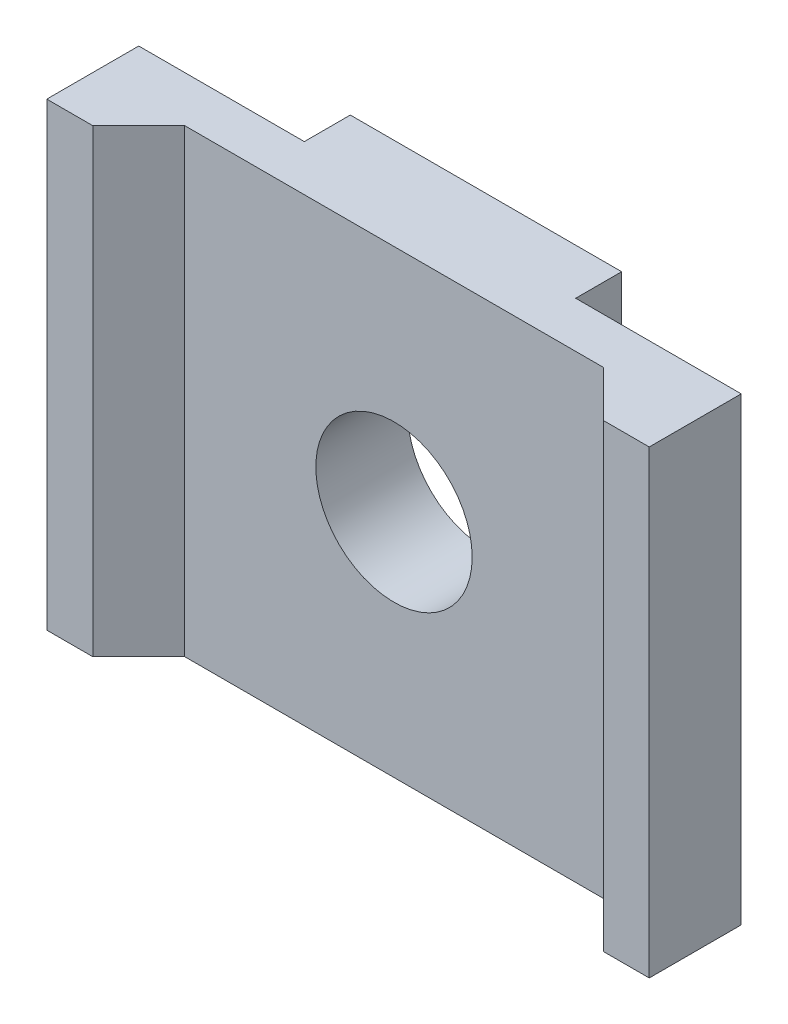
SolidWorks part; units mm, degrees
material "ABS"
ref_plane "Ebene vorne" through (0, 0, 0) normal (0, 0, 1) x (1, 0, 0)
ref_plane "Ebene oben" through (0, 0, 0) normal (0, 1, 0) x (1, 0, 0)
ref_plane "Ebene rechts" through (0, 0, 0) normal (1, 0, 0) x (0, 0, -1)
sketch "Skizze1" plane through (0, 0, 0) normal (0, 1, 0) x (1, 0, 0)
  line L0 (0, 0) -> (-4.55, 0)
  line L1 (-4.55, 0) -> (-4.55, -1)
  line L2 (-4.55, -1) -> (-6.55, -1)
  line L3 (-6.55, -1) -> (-6.55, 1)
  line L4 (-6.55, 1) -> (-2.95, 1)
  line L5 (-2.95, 1) -> (-2.95, 2)
  line L6 (-2.95, 2) -> (0, 2)
  line L7 (0, 2) -> (0, 0)
  dimension "D1" = 2.95
  dimension "D2" = 4.55
  dimension "D3" = 1
  dimension "D4" = 1
  dimension "D5" = 1
  dimension "D6" = 2
extrude "Aufsatz-Linear austragen1" add sketch "Skizze1" along normal blind 10
mirror "Spiegeln1" about plane through (0, 10, -2) normal (-1, 0, 0) of bodies 101
hole_wizard "Durchgangsloch für M31" positions "Skizze2" profile "Skizze3" hole size "M3" standard "DIN" end condition through all
sketch "Skizze2" plane through (0, 0, 0) normal (0, 0, 1) x (1, 0, 0)
  line L0 (0, 0) -> (0, 10) construction
  line L1 (-4.55, 10) -> (4.55, 10) construction
  point P7 (0, 5)
sketch "Skizze3" plane through (0, 5, 0) normal (1, 0, 0) x (0, -1, 0)
  line L0 (0, 0) -> (0, 2)
  line L1 (0, 2) -> (1.7, 2)
  line L2 (1.7, 2) -> (1.7, 0)
  line L5 (1.7, 0) -> (0, 0)
  line L11 (0, -6.35) -> (0, 107.95) construction
  dimension "Bohrerdurchmesser" = 3.4
  dimension "Bohrungstiefe" = 2
draft "Formschräge1" type of draft neutral plane draft angle 45 faces to draft 2 face at (4.55, 5, 0.5) face at (-4.55, 5, 0.5) neutral plane through (0, 10, 0) neutral plane normal (0, 0, 1) parameters "D1"=45
pattern_linear "Lineares Muster1" [suppressed] count 10 spacing 10
combine bodies "Kombinieren1" [suppressed] operation type add bodies to combine 103 104 105 106 107 108 109 110 111 112 114 115 116 117 119 118 120 121 122 123
